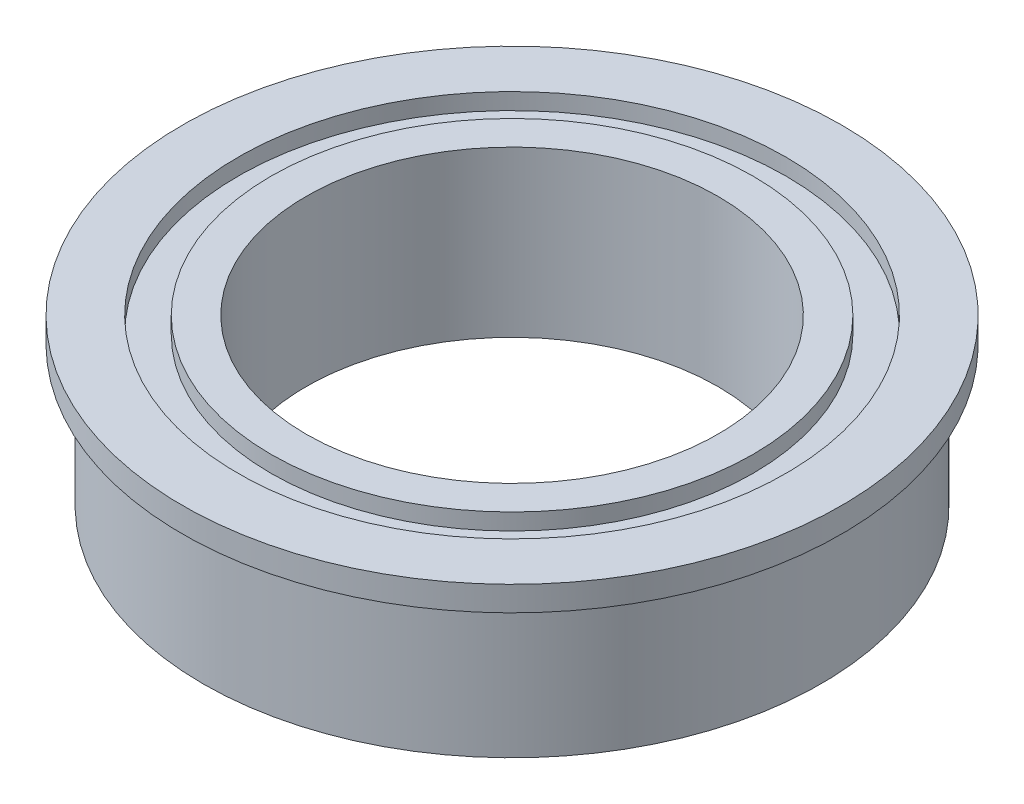
SolidWorks part; units mm, degrees
material "AISI 304"
ref_plane "Front Plane" through (0, 0, 0) normal (0, 0, 1) x (1, 0, 0)
ref_plane "Top Plane" through (0, 0, 0) normal (0, 1, 0) x (1, 0, 0)
ref_plane "Right Plane" through (0, 0, 0) normal (1, 0, 0) x (0, 0, -1)
sketch "Sketch1" plane through (0, 0, 0) normal (0, 0, 1) x (1, 0, 0)
  line L0 (0, 0) -> (0, 26.086) construction
  line L1 (0, 0) -> (5, 0) construction
  line L2 (5, 0.6) -> (5, -3.4)
  line L3 (5, -3.4) -> (5.85, -3.4)
  line L4 (5.85, -3.4) -> (5.85, -3)
  line L5 (5.85, -3) -> (6.65, -3)
  line L6 (6.65, -3) -> (6.65, -3.4)
  line L7 (6.65, -3.4) -> (7.5, -3.4)
  line L8 (7.5, -3.4) -> (7.5, 0)
  line L9 (7.5, 0) -> (8, 0)
  line L10 (8, 0) -> (8, 0.6)
  line L11 (8, 0.6) -> (6.65, 0.6)
  line L12 (6.65, 0.6) -> (6.65, 0.2)
  line L13 (6.65, 0.2) -> (5.85, 0.2)
  line L14 (5.85, 0.2) -> (5.85, 0.6)
  line L15 (5.85, 0.6) -> (5, 0.6)
  dimension "D1" = 10
  dimension "D2" = 4
  dimension "D3" = 0.6
  dimension "D4" = 0.8
  dimension "D5" = 15
  dimension "D6" = 16
  dimension "D7" = 0.4
revolve "Revolve1" add sketch "Sketch1" angle 360 about L0
